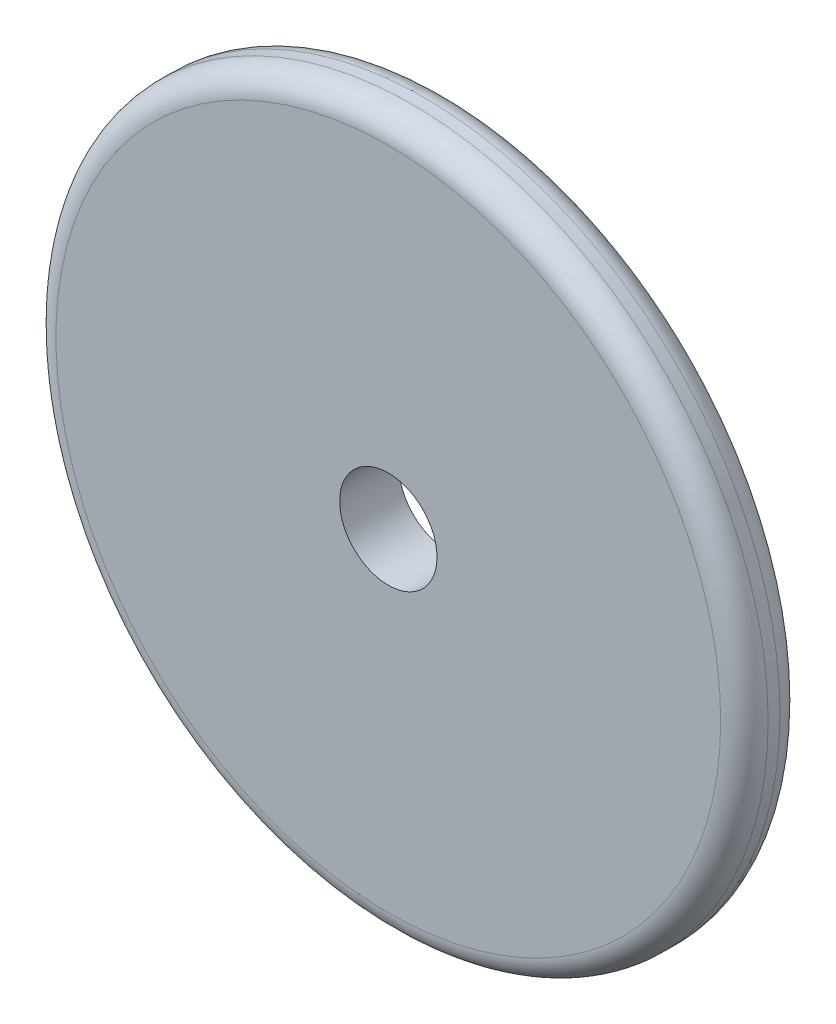
SolidWorks part; units mm, degrees
material "PA Typ 6"
ref_plane "Ebene vorne" through (0, 0, 0) normal (0, 0, 1) x (1, 0, 0)
ref_plane "Ebene oben" through (0, 0, 0) normal (0, 1, 0) x (1, 0, 0)
ref_plane "Ebene rechts" through (0, 0, 0) normal (1, 0, 0) x (0, 0, -1)
sketch "Skizze1" plane through (0, 0, 0) normal (0, 0, 1) x (1, 0, 0)
  circle A0 centre (0, 0) radius 4.1
  circle A1 centre (0, 0) radius 30
  dimension "D1" = 8.2
  dimension "D2" = 60
extrude "Aufsatz-Linear austragen1" add sketch "Skizze1" along normal mid plane 5
fillet "Verrundung1" radius 2 2 edges at (30, 0, -2.5) (30, 0, 2.5)
